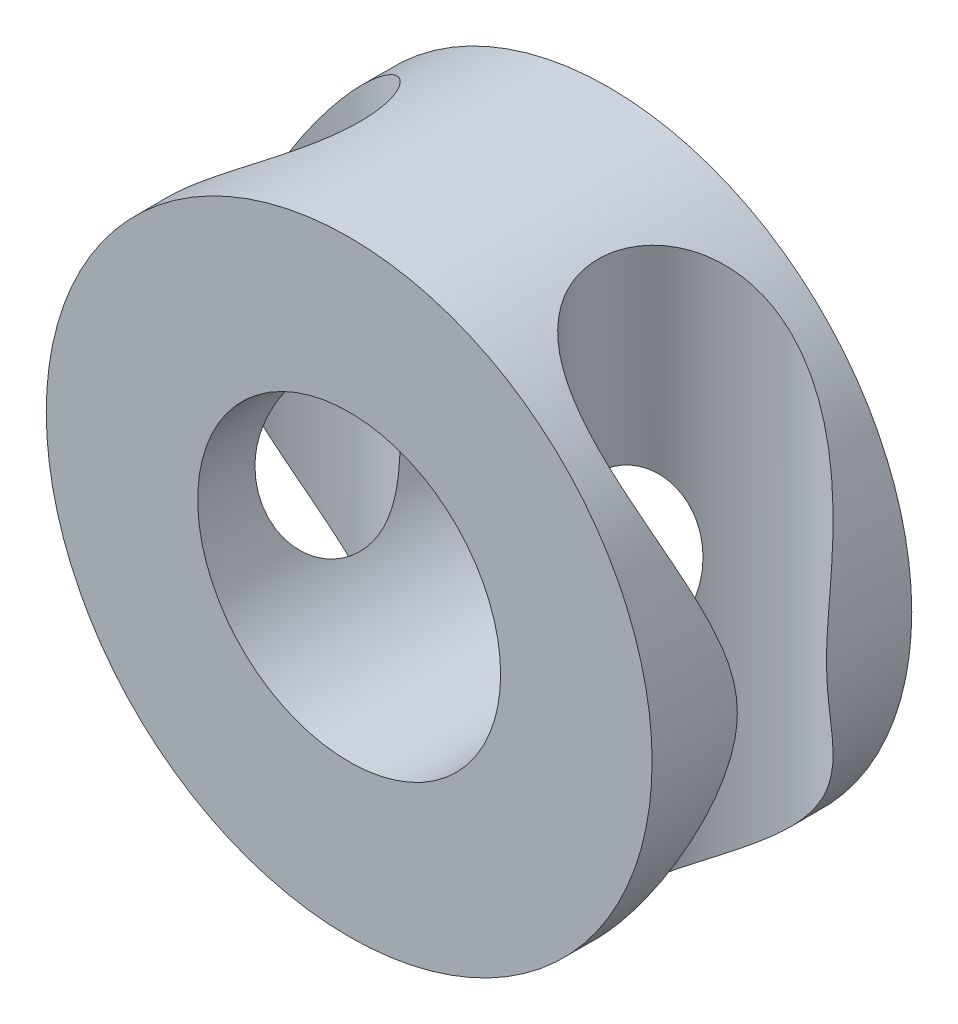
SolidWorks part; units mm, degrees
ref_plane "Plan de face" through (0, 0, 0) normal (0, 0, 1) x (1, 0, 0)
ref_plane "Plan de dessus" through (0, 0, 0) normal (0, 1, 0) x (1, 0, 0)
ref_plane "Plan de droite" through (0, 0, 0) normal (1, 0, 0) x (0, 0, -1)
sketch "Esquisse1" plane through (0, 0, 0) normal (0, 0, 1) x (1, 0, 0)
  circle A0 centre (0, 0) radius 7
  circle A1 centre (0, 0) radius 3.5
extrude "Extrusion1" add sketch "Esquisse1" along normal blind 6
ref_plane "Plan1" through (0, 7, 0) normal (0, 1, 0) x (-1, 0, 0)
sketch "Esquisse3" plane through (0, 7, 0) normal (0, 1, 0) x (-1, 0, 0)
  line L0 (0, 0) -> (0, 6) construction
  line L1 (7, 6) -> (-7, 6) construction
  line L2 (0, 3) -> (-7, 3) construction
  line L3 (-7, 6) -> (-7, 0) construction
  circle A0 centre (5, 3) radius 2.25
  circle A1 centre (-5, 3) radius 2.25
extrude "Extrusion4" cut sketch "Esquisse3" against normal through all
